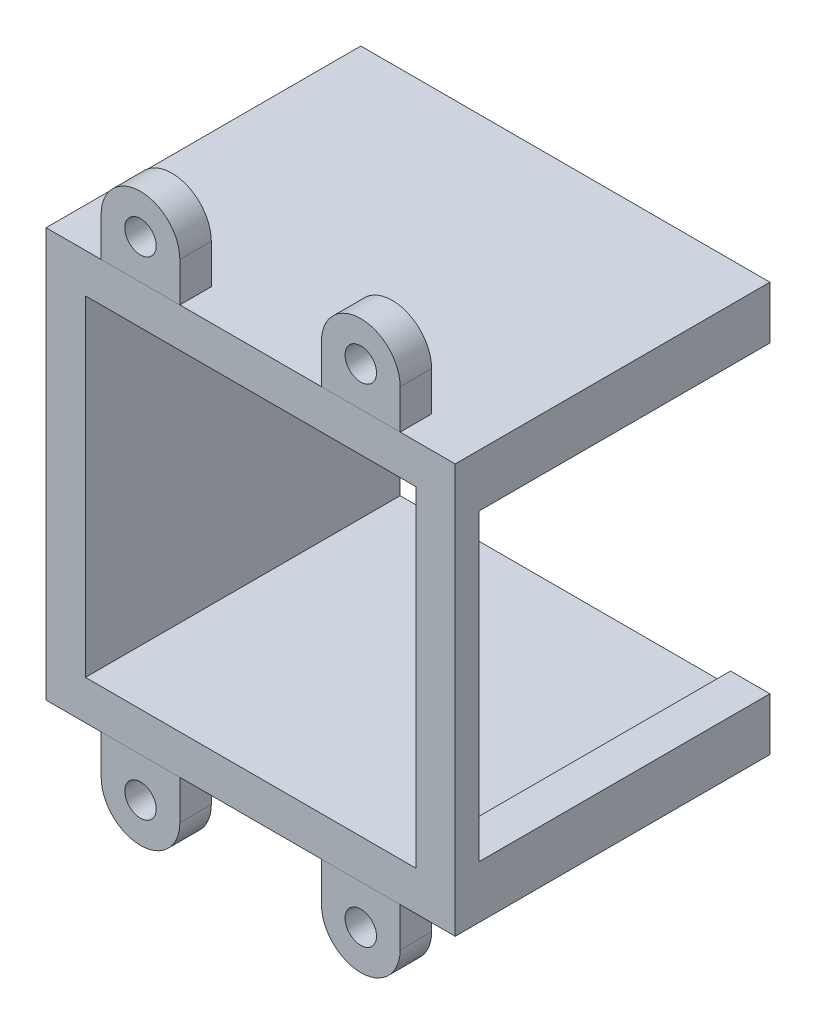
SolidWorks part; units mm, degrees
ref_plane "前基準面" through (0, 0, 0) normal (0, 0, 1) x (1, 0, 0)
ref_plane "上基準面" through (0, 0, 0) normal (0, 1, 0) x (1, 0, 0)
ref_plane "右基準面" through (0, 0, 0) normal (1, 0, 0) x (0, 0, -1)
sketch "草圖1" plane through (0, 0, 0) normal (0, 0, 1) x (1, 0, 0)
  line L1 (-21, -21) -> (21, -21)
  line L2 (-21, -21) -> (-21, 21)
  line L3 (-21, 21) -> (21, 21)
  line L4 (21, -21) -> (21, 21)
  line L5 (-21, -21) -> (21, 21) construction
  line L6 (-21, 21) -> (21, -21) construction
  point P0 (0, 0)
  dimension "D1" = 42
  dimension "D2" = 42
sketch "草圖2" plane through (0, 0, 0) normal (0, 0, 1) x (1, 0, 0)
  line L1 (-26, -26) -> (26, -26)
  line L2 (-26, -26) -> (-26, 26)
  line L3 (-26, 26) -> (26, 26)
  line L4 (26, -26) -> (26, 26)
  line L5 (-26, -26) -> (26, 26) construction
  line L6 (-26, 26) -> (26, -26) construction
  point P0 (0, 0)
  dimension "D1" = 52
  dimension "D2" = 52
extrude "填料-伸長1" add sketch "草圖2" along normal blind 40
extrude "除料-伸長1" cut sketch "草圖1" along normal blind 40
sketch "草圖4" plane through (26, 0, 0) normal (1, 0, 0) x (0, 0, -1)
  line L0 (0, 19.3) -> (-37, 19.3)
  line L1 (0, -26) -> (0, 26) construction
  line L2 (-37, 19.3) -> (-37, -19.3)
  line L3 (-37, -19.3) -> (0, -19.3)
  line L4 (0, -19.3) -> (0, 19.3)
  line L5 (-40, -26) -> (-40, 26) construction
  line L6 (-40, 26) -> (0, 26) construction
  line L7 (-40, -26) -> (0, -26) construction
  dimension "D1" = 3
  dimension "D2" = 6.7
  dimension "D3" = 6.7
extrude "除料-伸長2" cut sketch "草圖4" against normal up to next
sketch "草圖5" plane through (0, 0, 40) normal (0, 0, 1) x (1, 0, 0)
  line L0 (26, 26) -> (-26, 26) construction
  line L1 (-19, 26) -> (-19, 31)
  line L3 (-9, 31) -> (-9, 26)
  line L4 (-9, 26) -> (-19, 26)
  line L5 (-21, 21) -> (-21, -21) construction
  line L6 (19, 31) -> (19, 26)
  line L7 (19, 26) -> (9, 26)
  line L8 (9, 26) -> (9, 31)
  line L9 (0, 0) -> (-86.1494, 0) construction
  line L10 (9, -26) -> (9, -31)
  line L11 (19, -26) -> (9, -26)
  line L12 (19, -31) -> (19, -26)
  line L13 (-9, -26) -> (-19, -26)
  line L14 (-9, -31) -> (-9, -26)
  line L15 (-19, -26) -> (-19, -31)
  arc A0 (-19, 31) -> (-9, 31) centre (-14, 31) cw
  circle A1 centre (-14, 31) radius 2
  arc A2 (9, 31) -> (19, 31) centre (14, 31) cw
  circle A3 centre (14, 31) radius 2
  circle A4 centre (14, -31) radius 2
  arc A5 (9, -31) -> (19, -31) centre (14, -31) ccw
  circle A6 centre (-14, -31) radius 2
  arc A7 (-19, -31) -> (-9, -31) centre (-14, -31) ccw
  dimension "D3" = 2
  dimension "D1" = 10
  dimension "D2" = 5
  dimension "D4" = 2
extrude "填料-伸長2" add sketch "草圖5" against normal blind 4 separate body
